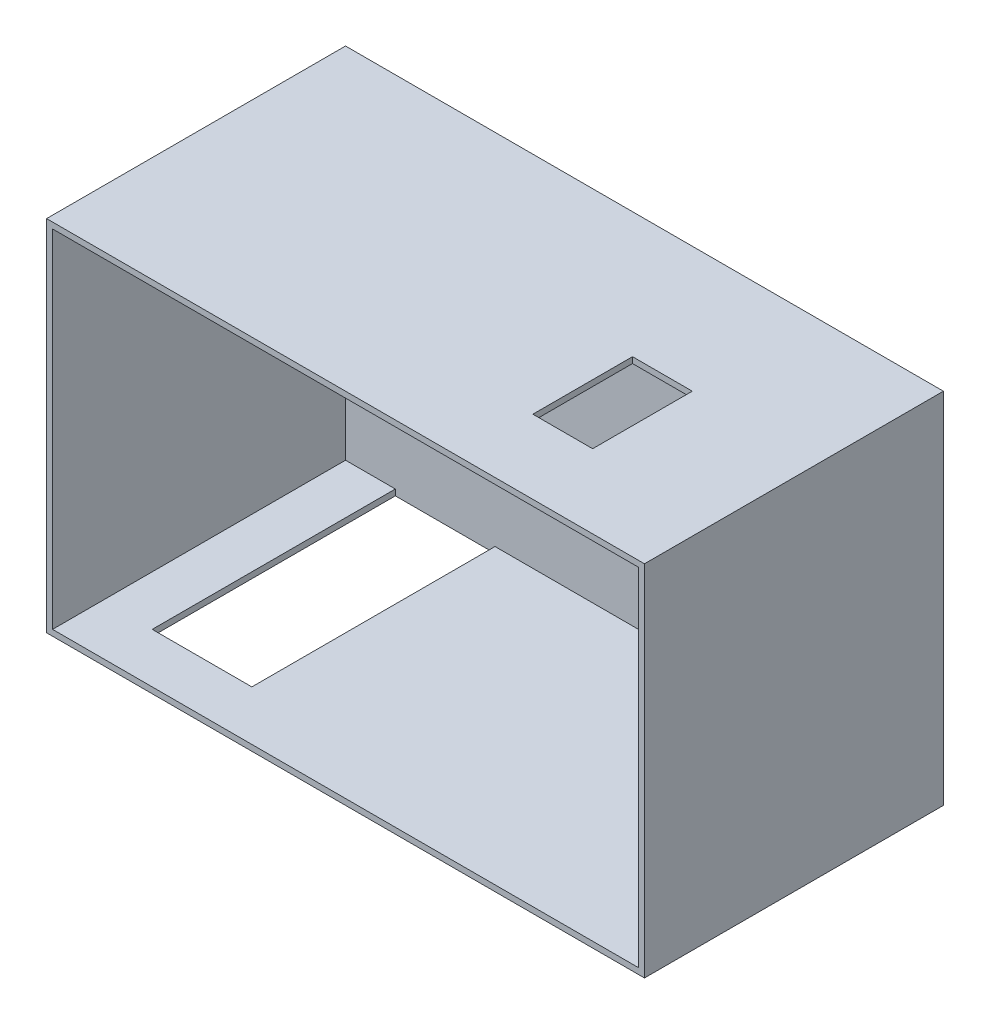
SolidWorks part; units mm, degrees
ref_plane "Plan de face" through (0, 0, 0) normal (0, 0, 1) x (1, 0, 0)
ref_plane "Plan de dessus" through (0, 0, 0) normal (0, 1, 0) x (1, 0, 0)
ref_plane "Plan de droite" through (0, 0, 0) normal (1, 0, 0) x (0, 0, -1)
sketch "Esquisse1" plane through (0, 0, 0) normal (0, 0, 1) x (1, 0, 0)
  line L1 (0, 0) -> (-300, 0)
  line L2 (0, 0) -> (0, 180)
  line L3 (0, 180) -> (-300, 180)
  line L4 (-300, 0) -> (-300, 180)
  dimension "D1" = 300
  dimension "D2" = 180
extrude "Boss.-Extru.1" add sketch "Esquisse1" along normal blind 150
shell "Coque1" thickness 3
sketch "Esquisse2" plane through (0, 3, 0) normal (0, 1, 0) x (1, 0, 0)
  line L0 (-297, -3) -> (-3, -3) construction
  line L1 (-272, -3) -> (-222, -3)
  line L2 (-272, -3) -> (-272, -125)
  line L3 (-272, -125) -> (-222, -125)
  line L4 (-222, -3) -> (-222, -125)
  line L5 (-297, -150) -> (-297, -3) construction
  line L6 (-297, -150) -> (-3, -150) construction
  dimension "D1" = 25
  dimension "D2" = 25
  dimension "D3" = 50
extrude "Enlèv. mat.-Extru.1" cut sketch "Esquisse2" against normal up to next
sketch "Esquisse3" plane through (0, 177, 0) normal (0, -1, 0) x (1, 0, 0)
  line L0 (-3, 3) -> (-297, 3) construction
  line L1 (-63, 113) -> (-93, 113)
  line L2 (-63, 113) -> (-63, 63)
  line L3 (-63, 63) -> (-93, 63)
  line L4 (-93, 113) -> (-93, 63)
  line L5 (-3, 150) -> (-3, 3) construction
  dimension "D1" = 30
  dimension "D2" = 60
  dimension "D3" = 60
  dimension "D4" = 50
extrude "Enlèv. mat.-Extru.2" cut sketch "Esquisse3" against normal up to next
